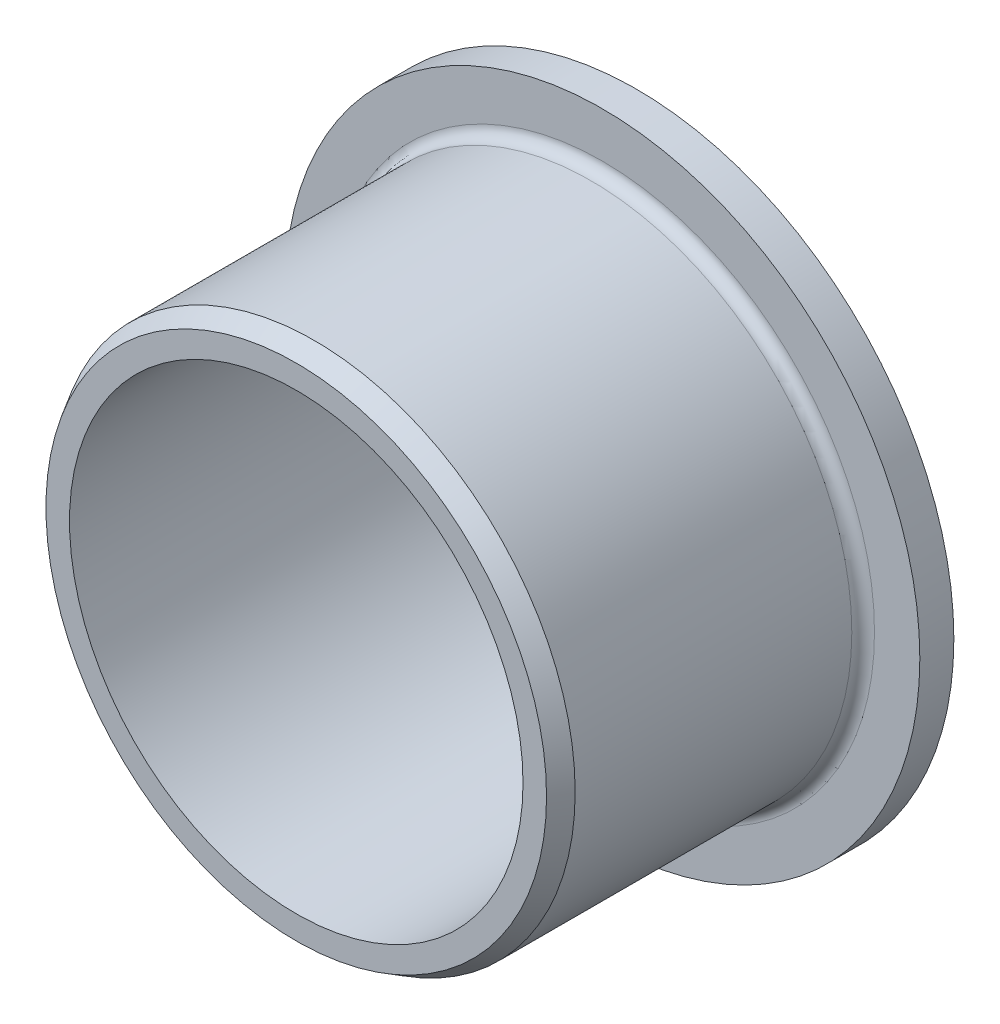
SolidWorks part; units mm, degrees
ref_plane "Płaszczyzna przednia" through (0, 0, 0) normal (0, 0, 1) x (1, 0, 0)
ref_plane "Płaszczyzna górna" through (0, 0, 0) normal (0, 1, 0) x (1, 0, 0)
ref_plane "Płaszczyzna prawa" through (0, 0, 0) normal (1, 0, 0) x (0, 0, -1)
sketch "Szkic1" plane through (0, 0, 0) normal (0, 0, 1) x (1, 0, 0)
  circle A0 centre (0, 0) radius 11.5
  dimension "D1" = 23
extrude "Wyciągnięcie-cienka ścianka1" add sketch "Szkic1" along normal blind 1.5 thin
sketch "Szkic2" plane through (0, 0, 0) normal (0, 0, 1) x (1, 0, 0)
  circle A0 centre (0, 0) radius 10
  circle A1 centre (0, 0) radius 11.5 construction
  circle A2 centre (0, 0) radius 11.5
  dimension "D1" = 20
extrude "Dodanie-wyciągnięcie1" add sketch "Szkic2" along normal blind 15
fillet "Zaokrąglenie1" radius 0.5 1 edges at (11.5, 0, 1.5)
chamfer "Sfazowanie1" distance 0.8 angle 30 1 edges at (11.5, 0, 15)
